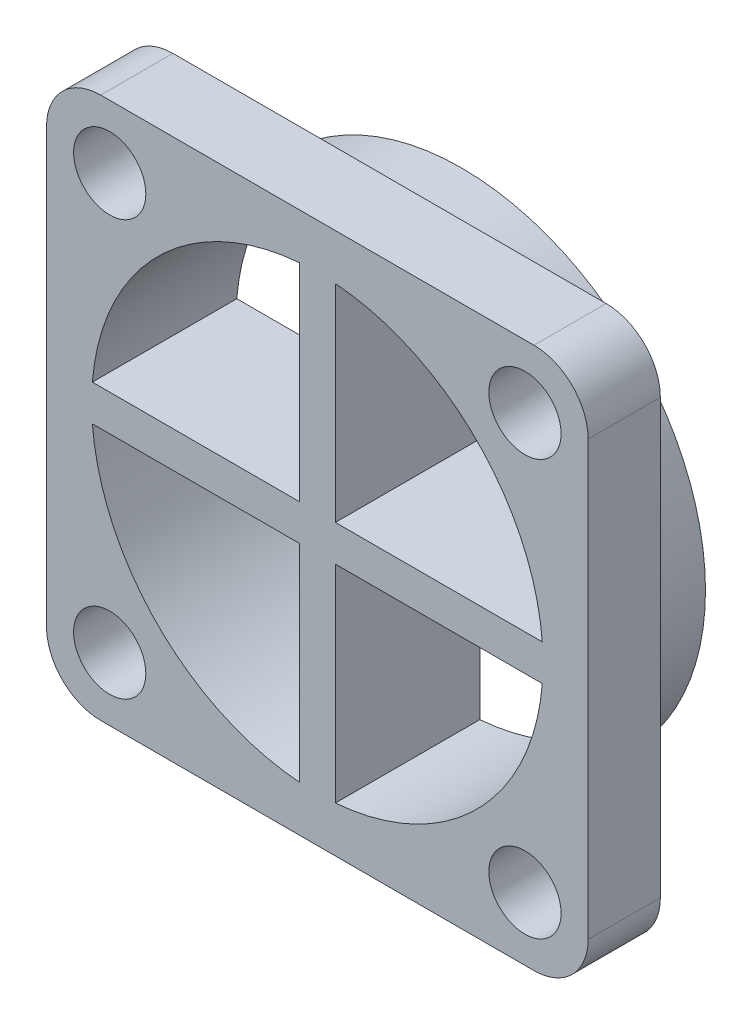
SolidWorks part; units mm, degrees
ref_plane "Front Plane" through (0, 0, 0) normal (0, 0, 1) x (1, 0, 0)
ref_plane "Top Plane" through (0, 0, 0) normal (0, 1, 0) x (1, 0, 0)
ref_plane "Right Plane" through (0, 0, 0) normal (1, 0, 0) x (0, 0, -1)
sketch "Sketch1" plane through (0, 0, 0) normal (0, 0, 1) x (1, 0, 0)
  circle A0 centre (0, 0) radius 13.5
  dimension "D1" = 27
extrude "Boss-Extrude1" add sketch "Sketch1" along normal blind 4
sketch "Sketch2" plane through (0, 0, 4) normal (0, 0, 1) x (1, 0, 0)
  line L1 (-15, 15) -> (15, 15)
  line L2 (-15, 15) -> (-15, -15)
  line L3 (-15, -15) -> (15, -15)
  line L4 (15, 15) -> (15, -15)
  line L5 (-15, 15) -> (15, -15) construction
  line L6 (-15, -15) -> (15, 15) construction
  point P0 (0, 0)
  dimension "D1" = 30
  dimension "D2" = 30
extrude "Boss-Extrude2" add sketch "Sketch2" along normal blind 4
fillet "Fillet1" radius 3 4 edges at (15, -15, 6) (-15, -15, 6) (-15, 15, 6) (15, 15, 6)
sketch "Sketch3" plane through (0, 0, 0) normal (0, 0, -1) x (-1, 0, 0)
  line L0 (1, -1) -> (12.4599, -1)
  line L1 (-12.4599, 1) -> (-1, 1)
  line L2 (-1, -1) -> (-1, -12.4599)
  line L3 (-12.4599, -1) -> (-1, -1)
  line L5 (-12.4599, 1) -> (12.4599, -1) construction
  line L6 (-12.4599, -1) -> (12.4599, 1) construction
  line L8 (-1, 12.4599) -> (-1, 1)
  line L9 (-0.0803, -1) -> (0.0803, -1)
  line L10 (1, 12.4599) -> (1, 1)
  line L11 (-1, 12.4599) -> (1, -12.4599) construction
  line L12 (-1, -12.4599) -> (1, 12.4599) construction
  line L13 (1, 1) -> (12.4599, 1)
  line L14 (-0.0803, 1) -> (0.0803, 1)
  line L15 (-1, 0.0803) -> (-1, -0.0803)
  line L16 (1, -1) -> (1, -12.4599)
  line L17 (1, 0.0803) -> (1, -0.0803)
  arc A0 (1, -12.4599) -> (12.4599, -1) centre (0, 0) ccw
  arc A1 (-12.4599, -1) -> (-1, -12.4599) centre (0, 0) ccw
  arc A2 (12.4599, 1) -> (1, 12.4599) centre (0, 0) ccw
  arc A3 (-1, 12.4599) -> (-12.4599, 1) centre (0, 0) ccw
  dimension "D1" = 25
  dimension "D2" = 2
  dimension "D3" = 2
sketch "Sketch4" plane through (0, 0, 0) normal (0, 0, -1) x (-1, 0, 0)
  line L0 (-12.4599, 1) -> (-1, 1)
  line L1 (-1, 1) -> (-1, 12.4599)
  arc A0 (-1, 12.4599) -> (-12.4599, 1) centre (0, 0) ccw
extrude "Cut-Extrude1" cut sketch "Sketch4" along normal blind 8 and the other way through all
mirror "Mirror1" about plane through (0, 0, 0) normal (1, 0, 0) of "Cut-Extrude1"
mirror "Mirror2" about plane through (0, 0, 0) normal (0, 1, 0) of "Mirror1", "Cut-Extrude1"
sketch "Sketch5" plane through (0, 0, 4) normal (0, 0, -1) x (-1, 0, 0)
  circle A0 centre (-11.5, 11.5) radius 2
  dimension "D1" = 4
  dimension "D2" = 11.5
  dimension "D3" = 11.5
extrude "Cut-Extrude2" cut sketch "Sketch5" against normal blind 8
mirror "Mirror3" about plane through (0, 0, 0) normal (0, 1, 0) of "Cut-Extrude2"
mirror "Mirror4" about plane through (0, 0, 0) normal (1, 0, 0) of "Mirror3", "Cut-Extrude2"
